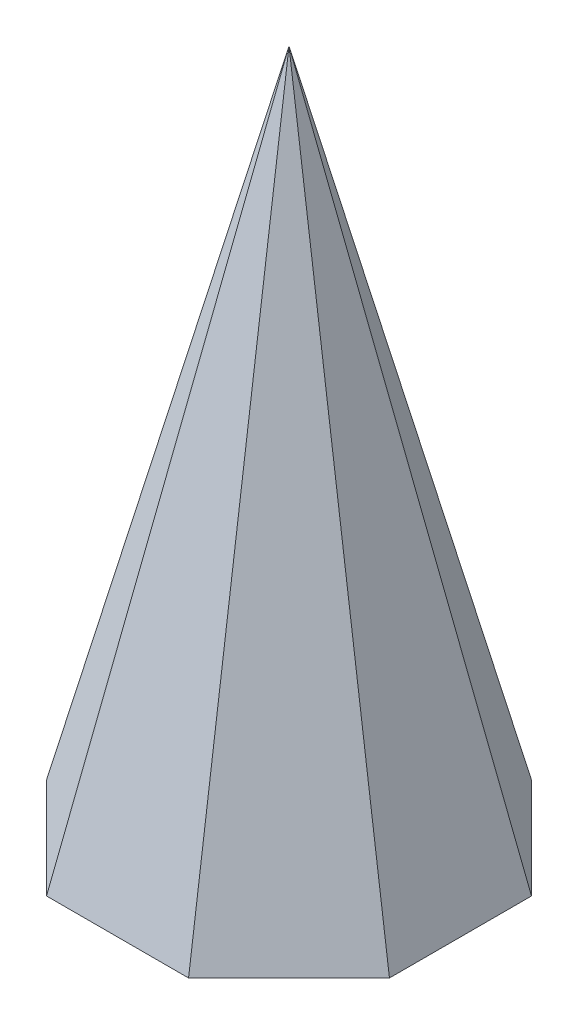
SolidWorks part; units mm, degrees
ref_plane "Front" through (0, 0, 0) normal (0, 0, 1) x (1, 0, 0)
ref_plane "Top" through (0, 0, 0) normal (0, 1, 0) x (1, 0, 0)
ref_plane "Right" through (0, 0, 0) normal (1, 0, 0) x (0, 0, -1)
sketch "Sketch1" plane through (0, 0, 0) normal (0, 1, 0) x (1, 0, 0)
  line L1 (2.0711, -5) -> (5, -2.0711)
  line L2 (5, -2.0711) -> (5, 2.0711)
  line L3 (5, 2.0711) -> (2.0711, 5)
  line L4 (2.0711, 5) -> (-2.0711, 5)
  line L5 (-2.0711, 5) -> (-5, 2.0711)
  line L6 (-5, 2.0711) -> (-5, -2.0711)
  line L7 (-5, -2.0711) -> (-2.0711, -5)
  line L8 (-2.0711, -5) -> (2.0711, -5)
  circle A0 centre (0, 0) radius 5 construction
  dimension "D1" = 10
sketch "Sketch2" plane through (0, 0, 0) normal (0, 0, 1) x (1, 0, 0)
  point P0 (0, 20)
  dimension "D1" = 20
loft "Loft1" add profiles "Sketch2", "Sketch1"
